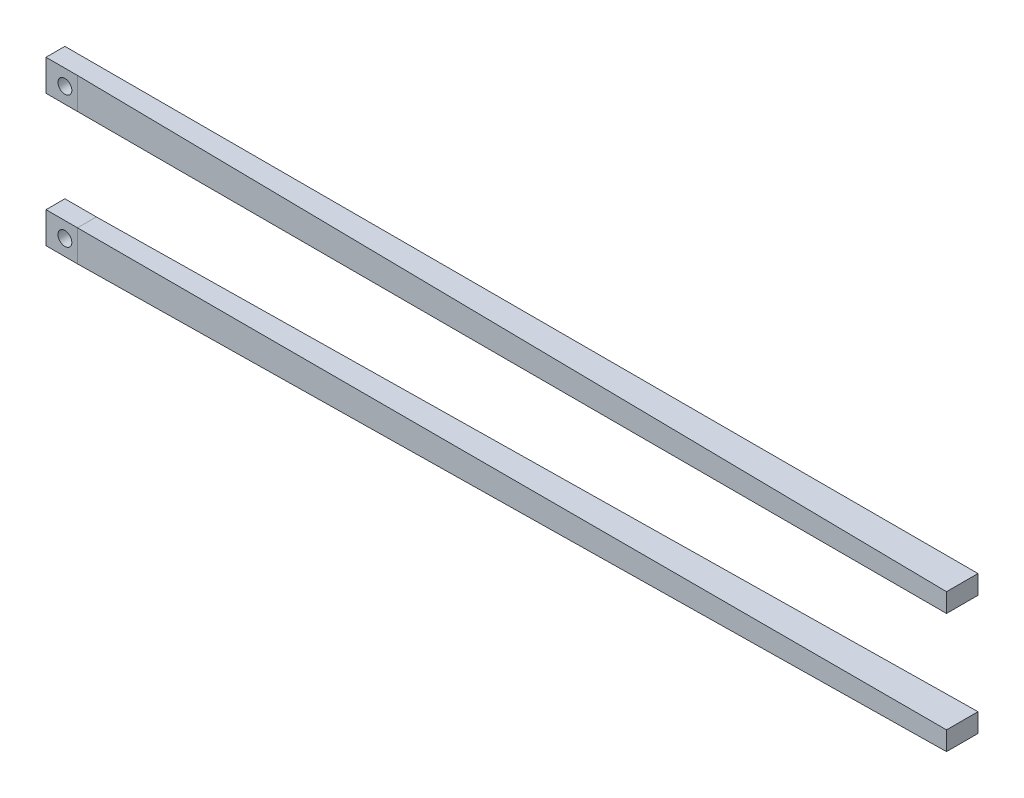
SolidWorks part; units mm, degrees
ref_plane "Ebene vorne" through (0, 0, 0) normal (0, 0, 1) x (1, 0, 0)
ref_plane "Ebene oben" through (0, 0, 0) normal (0, 1, 0) x (1, 0, 0)
ref_plane "Ebene rechts" through (0, 0, 0) normal (1, 0, 0) x (0, 0, -1)
sketch "Skizze1" plane through (0, 0, 0) normal (0, 0, 1) x (1, 0, 0)
  line L1 (0, 0) -> (5, 0)
  line L2 (0, 0) -> (0, -4.96)
  line L3 (0, -4.96) -> (5, -4.96)
  line L4 (5, 0) -> (5, -4.96)
  line L5 (0, -20.96) -> (5, -20.96)
  line L6 (0, -20.96) -> (0, -25.92)
  line L7 (0, -25.92) -> (5, -25.92)
  line L8 (5, -20.96) -> (5, -25.92)
  dimension "D1" = 4.96
  dimension "D2" = 4.96
  dimension "D3" = 5
  dimension "D4" = 5
  dimension "D5" = 16
extrude "Aufsatz-Linear austragen1" add sketch "Skizze1" along normal blind 3
hole_wizard "Durchgangsloch für M21" positions "Skizze3" profile "Skizze2" hole size "M2" standard "ANSI Metrisch"
sketch "Skizze3" plane through (0, 0, 3) normal (0, 0, 1) x (1, 0, 0)
  line L0 (0, 0) -> (0, -4.96) construction
  line L1 (5, 0) -> (0, 0) construction
  line L2 (0, -25.92) -> (5, -25.92) construction
  line L3 (0, -20.96) -> (0, -25.92) construction
  point P0 (3, -2.5)
  point P2 (3, -23.42)
  dimension "D1" = 3
  dimension "D2" = 2.5
  dimension "D3" = 2.5
  dimension "D4" = 3
sketch "Skizze2" plane through (3, -2.5, 3) normal (1, 0, 0) x (0, -1, 0)
  line L0 (0, 0) -> (0, 3.6609)
  line L1 (0, 3.6609) -> (1.1, 3)
  line L2 (1.1, 3) -> (1.1, 0)
  line L5 (1.1, 0) -> (0, 0)
  line L10 (0, 3.6609) -> (-1.1, 3) construction
  line L11 (0, -6.35) -> (0, 107.95) construction
  dimension "Bohrerdurchmesser" = 2.2
  dimension "Bohrungstiefe" = 3
  dimension "Spitzenwinkel" = 118
ref_plane "Ebene1" through (145, 0, 0) normal (1, 0, 0) x (0, 0, -1)
sketch "Skizze6" plane through (145, 0, 0) normal (1, 0, 0) x (0, 0, -1)
  line L1 (0, 0) -> (-5, 0)
  line L2 (0, 0) -> (0, -3)
  line L3 (0, -3) -> (-5, -3)
  line L4 (-5, 0) -> (-5, -3)
  line L5 (-5, -19) -> (0, -19)
  line L6 (-5, -19) -> (-5, -22)
  line L7 (-5, -22) -> (0, -22)
  line L8 (0, -19) -> (0, -22)
  dimension "D1" = 5
  dimension "D2" = 3
  dimension "D3" = 16
  dimension "D4" = 3
loft "Ausformung1" add section face at (5, -23.44, 1.5) section "Skizze6"
sketch "Skizze7" plane through (145, 0, 0) normal (1, 0, 0) x (0, 0, -1)
  line L1 (-5, -3) -> (0, -3)
  line L2 (-5, -3) -> (-5, 0)
  line L3 (-5, 0) -> (0, 0)
  line L4 (0, -3) -> (0, 0)
  dimension "D1" = 3
  dimension "D2" = 5
  dimension "D3" = 16
  dimension "D4" = 16
loft "Ausformung3" add profiles "Skizze7" section face at (5, -2.48, 1.5) section "Skizze7"
